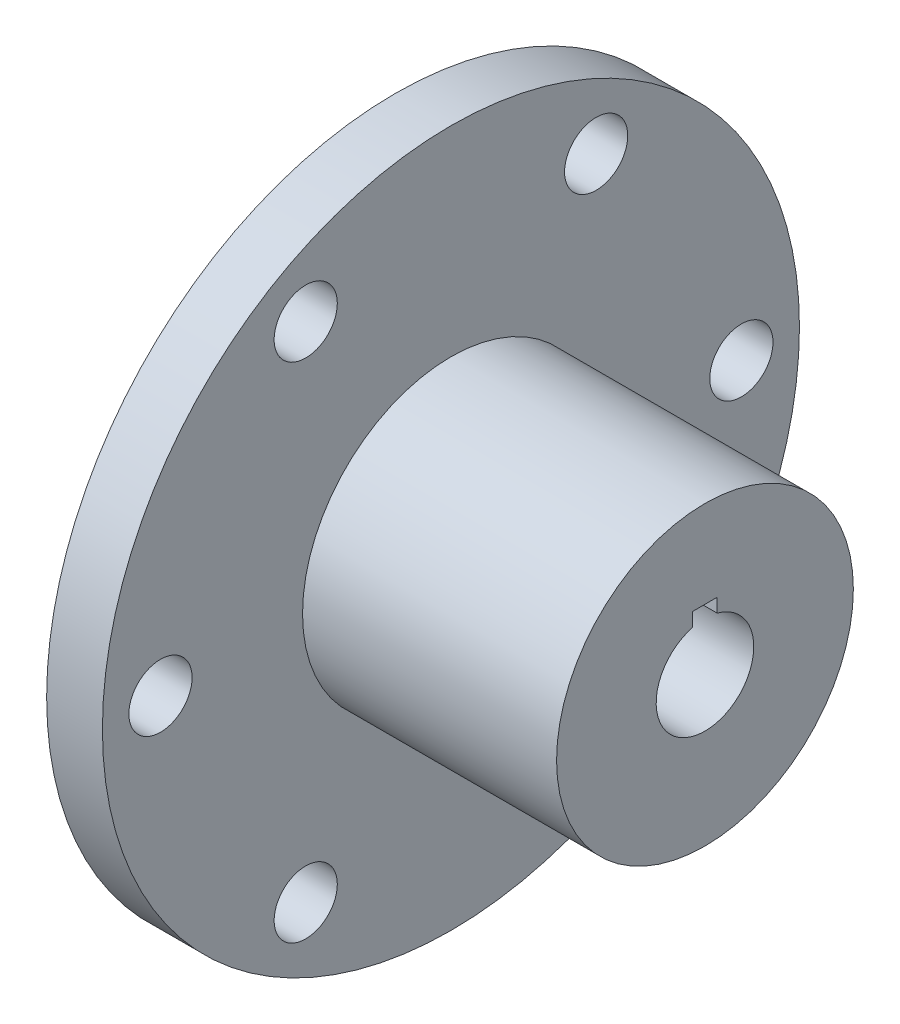
SolidWorks part; units mm, degrees
ref_plane "Front Plane" through (0, 0, 0) normal (0, 0, 1) x (1, 0, 0)
ref_plane "Top Plane" through (0, 0, 0) normal (0, 1, 0) x (1, 0, 0)
ref_plane "Right Plane" through (0, 0, 0) normal (1, 0, 0) x (0, 0, -1)
sketch "Sketch1" plane through (0, 0, 0) normal (0, 0, 1) x (1, 0, 0)
  line L0 (-17.6071, 28.575) -> (-17.6071, 0)
  line L1 (-17.6071, 0) -> (-13.0351, 0)
  line L2 (-13.0351, 0) -> (-13.0351, 28.575)
  line L3 (-13.0351, 28.575) -> (-17.6071, 28.575)
  line L4 (-17.6071, 0) -> (-13.0351, 0) construction
revolve "Revolve1" add sketch "Sketch1" angle 360 about L4
sketch "Sketch2" plane through (-13.0351, 0, 0) normal (1, 0, 0) x (0, 0, -1)
  circle A0 centre (0, 0) radius 12.1666
extrude "Boss-Extrude1" add sketch "Sketch2" along normal blind 20.828
sketch "Sketch3" plane through (-17.6071, 0, 0) normal (-1, 0, 0) x (0, 0, 1)
  line L0 (1.0033, 3.8726) -> (1.0033, 5.0038)
  line L1 (1.0033, 5.0038) -> (-1.0033, 5.0038)
  line L2 (-1.0033, 5.0038) -> (-1.0033, 3.8726)
  arc A0 (-1.0033, 3.8726) -> (1.0033, 3.8726) centre (0, 0) cw
extrude "Cut-Extrude1" cut sketch "Sketch3" against normal through all
ref_plane "Plane1" through (0, 0, 0) normal (0, 0, -1) x (-1, 0, 0)
sketch "Sketch4" plane through (0, 0, 0) normal (0, 0, -1) x (-1, 0, 0)
  line L0 (-7.7929, 4.0005) -> (-7.7929, 0)
  line L1 (-7.7929, 0) -> (17.6071, 0)
  line L2 (17.6071, 0) -> (17.6071, 4.0005)
  line L3 (17.6071, 4.0005) -> (-7.7929, 4.0005)
  line L4 (-7.7929, 0) -> (17.6071, 0) construction
revolve "Cut-Revolve1" cut sketch "Sketch4" angle 360 about L4
hole_wizard "Hole1" positions "Sketch6" profile "Sketch5" legacy
sketch "Sketch6" plane through (-17.6071, 0, 0) normal (-1, 0, 0) x (0, 0, 1)
  point P0 (23.8125, 0)
  point P1 (11.9062, 20.6222)
  point P2 (-11.9062, 20.6222)
  point P3 (-23.8125, 0)
  point P4 (-11.9062, -20.6222)
  point P5 (11.9062, -20.6222)
sketch "Sketch5" plane through (-17.6071, 0, 23.8125) normal (0, 1, 0) x (0, 0, 1)
  line L0 (0, 0) -> (0, 25.4)
  line L1 (0, 25.4) -> (2.5908, 25.4)
  line L2 (2.5908, 25.4) -> (2.5908, 0)
  line L3 (2.5908, 0) -> (0, 0)
  line L4 (0, 110) -> (0, -10) construction
  dimension "Diameter" = 5.1816
  dimension "Depth" = 25.4
